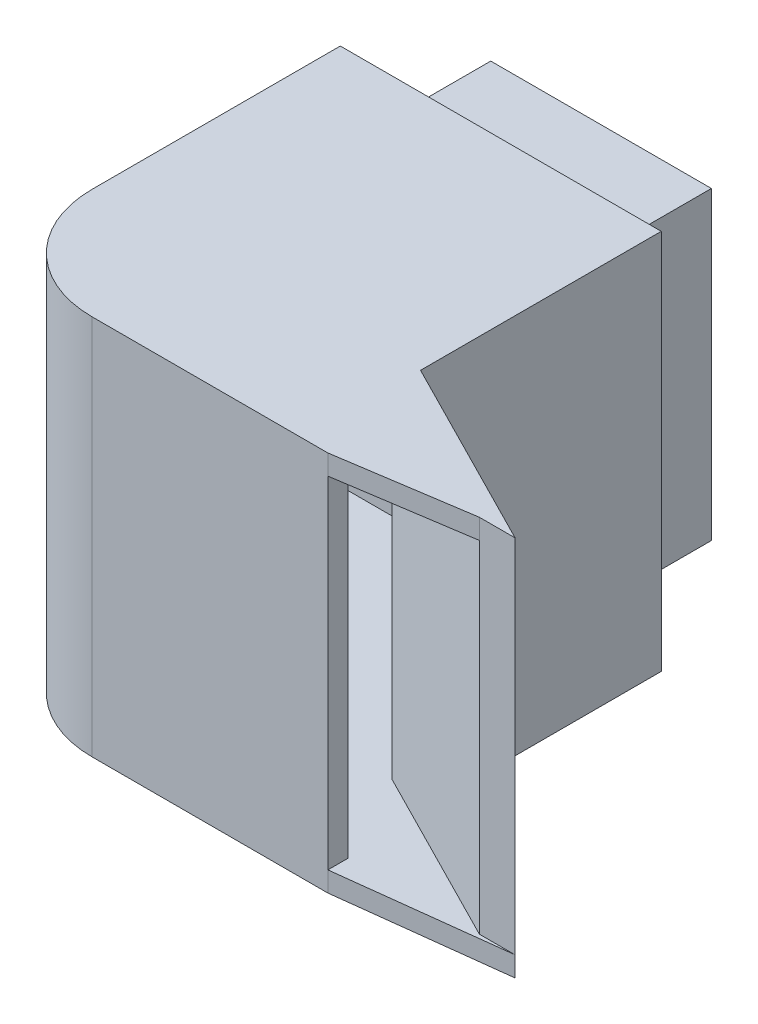
SolidWorks part; units mm, degrees
ref_plane "Front Plane" through (0, 0, 0) normal (0, 0, 1) x (1, 0, 0)
ref_plane "Top Plane" through (0, 0, 0) normal (0, 1, 0) x (1, 0, 0)
ref_plane "Right Plane" through (0, 0, 0) normal (1, 0, 0) x (0, 0, -1)
sketch "Sketch1" plane through (0, 0, 0) normal (0, 1, 0) x (1, 0, 0)
  line L0 (-13.0014, 4.911) -> (-13.0014, -7.089)
  line L1 (-13.0014, -7.089) -> (-3.4087, -11.9667)
  line L2 (-23.4946, -12.9667) -> (-11.7429, -12.9667)
  line L3 (-13.0014, 4.911) -> (-29.0014, 4.911)
  line L4 (-29.0014, 4.911) -> (-29.0014, -7.4598)
  line L5 (-11.7429, -12.9667) -> (-11.7429, -11.9667)
  line L6 (-11.7429, -11.9667) -> (-23.4876, -11.9667)
  line L7 (-28.0014, -7.4528) -> (-28.0014, 3.911)
  line L8 (-28.0014, 3.911) -> (-14.0671, 3.911)
  line L9 (-14.0671, 3.911) -> (-14.0671, -7.4528)
  line L10 (-14.0671, -7.4528) -> (-5.1899, -11.9667)
  line L11 (-5.1899, -11.9667) -> (-3.4087, -11.9667)
  arc A0 (-29.0014, -7.4598) -> (-23.4946, -12.9667) centre (-23.4946, -7.4598) ccw
  arc A1 (-23.4876, -11.9667) -> (-28.0014, -7.4528) centre (-23.4876, -7.4528) cw
  dimension "D3" = 1
  dimension "D1" = 12
  dimension "D2" = 16
  dimension "D4" = 1
  dimension "D5" = 1
extrude "Boss-Extrude1" add sketch "Sketch1" along normal blind 19
sketch "Sketch2" plane through (0, 19, 0) normal (0, 1, 0) x (1, 0, 0)
  line L0 (-29.0014, 4.911) -> (-13.0014, 4.911)
  line L1 (-13.0014, 4.911) -> (-13.0014, -7.089)
  line L2 (-13.0014, -7.089) -> (-3.4087, -11.9667)
  line L3 (-3.4087, -11.9667) -> (-5.1899, -11.9667)
  line L4 (-5.1899, -11.9667) -> (-11.7429, -12.9667)
  line L5 (-11.7429, -12.9667) -> (-23.4946, -12.9667)
  line L6 (-29.0014, -7.4598) -> (-29.0014, 4.911)
  arc A0 (-23.4946, -12.9667) -> (-29.0014, -7.4598) centre (-23.4946, -7.4598) cw
extrude "Boss-Extrude2" add sketch "Sketch2" against normal blind 1
sketch "Sketch3" plane through (0, 0, 0) normal (0, -1, 0) x (-1, 0, 0)
  line L0 (3.4087, -11.9667) -> (13.0014, -7.089)
  line L1 (13.0014, -7.089) -> (13.0014, 4.911)
  line L2 (13.0014, 4.911) -> (29.0014, 4.911)
  line L3 (29.0014, 4.911) -> (29.0014, -7.4598)
  line L4 (23.4946, -12.9667) -> (11.7429, -12.9667)
  line L5 (11.7429, -12.9667) -> (3.4087, -11.9667)
  line L6 (3.4087, -11.9667) -> (3.3684, -12.1084)
  arc A0 (29.0014, -7.4598) -> (23.4946, -12.9667) centre (23.4946, -7.4598) cw
  line M1 (29.0014, 4.911) -> (13.0014, 4.911)
  line M2 (13.0014, 4.911) -> (13.0014, -7.089)
  line M3 (13.0014, -7.089) -> (3.4087, -11.9667)
  line M4 (3.4087, -11.9667) -> (5.1899, -11.9667)
  line M5 (5.1899, -11.9667) -> (14.0671, -7.4528)
  line M6 (14.0671, -7.4528) -> (14.0671, 3.911)
  line M7 (14.0671, 3.911) -> (28.0014, 3.911)
  line M8 (28.0014, 3.911) -> (28.0014, -7.4528)
  arc M9 (28.0014, -7.4528) -> (23.4876, -11.9667) centre (23.4876, -7.4528) cw
  line M10 (23.4876, -11.9667) -> (11.7429, -11.9667)
  line M11 (11.7429, -11.9667) -> (11.7429, -12.9667)
  line M12 (11.7429, -12.9667) -> (23.4946, -12.9667)
  arc M13 (23.4946, -12.9667) -> (29.0014, -7.4598) centre (23.4946, -7.4598) ccw
  line M14 (29.0014, -7.4598) -> (29.0014, 4.911)
extrude "Boss-Extrude3" add sketch "Sketch3" against normal blind 1 contours M14 M1 M2 M3 M4 M5 M6 M7 M8 M9 M10 M11 M12 M13 | L5 M11 M10 M9 M8 M7 M6 M5 M4
sketch "Sketch4" plane through (0, 0, -4.911) normal (0, 0, -1) x (-1, 0, 0)
  line L0 (13.0014, 0) -> (29.0014, 0) construction
  line L1 (25.5014, 2.9) -> (16.5014, 2.9)
  line L2 (26.5014, 17.1) -> (15.5014, 17.1)
  line L3 (26.5014, 17.1) -> (26.5014, 1.9)
  line L4 (26.5014, 1.9) -> (15.5014, 1.9)
  line L5 (15.5014, 17.1) -> (15.5014, 1.9)
  line L6 (25.5014, 2.9) -> (25.5014, 16.1)
  line L7 (25.5014, 16.1) -> (16.5014, 16.1)
  line L8 (16.5014, 2.9) -> (16.5014, 16.1)
  line L9 (29.0014, 19) -> (29.0014, 0) construction
  point P4 (21.0014, 9.5)
  dimension "D1" = 11
  dimension "D2" = 15.2
  dimension "D3" = 1
  dimension "D4" = 1.9
  dimension "D5" = 2.5
  dimension "D6" = 1
  dimension "D7" = 1
  dimension "D8" = 1
extrude "Boss-Extrude4" add sketch "Sketch4" along normal blind 5
sketch "Sketch5" plane through (0, 0, -9.911) normal (0, 0, -1) x (-1, 0, 0)
  line L1 (25.5014, 2.9) -> (16.5014, 2.9)
  line L2 (25.5014, 2.9) -> (25.5014, 16.1)
  line L3 (25.5014, 16.1) -> (16.5014, 16.1)
  line L4 (16.5014, 2.9) -> (16.5014, 16.1)
extrude "Cut-Extrude1" cut sketch "Sketch5" against normal blind 13
